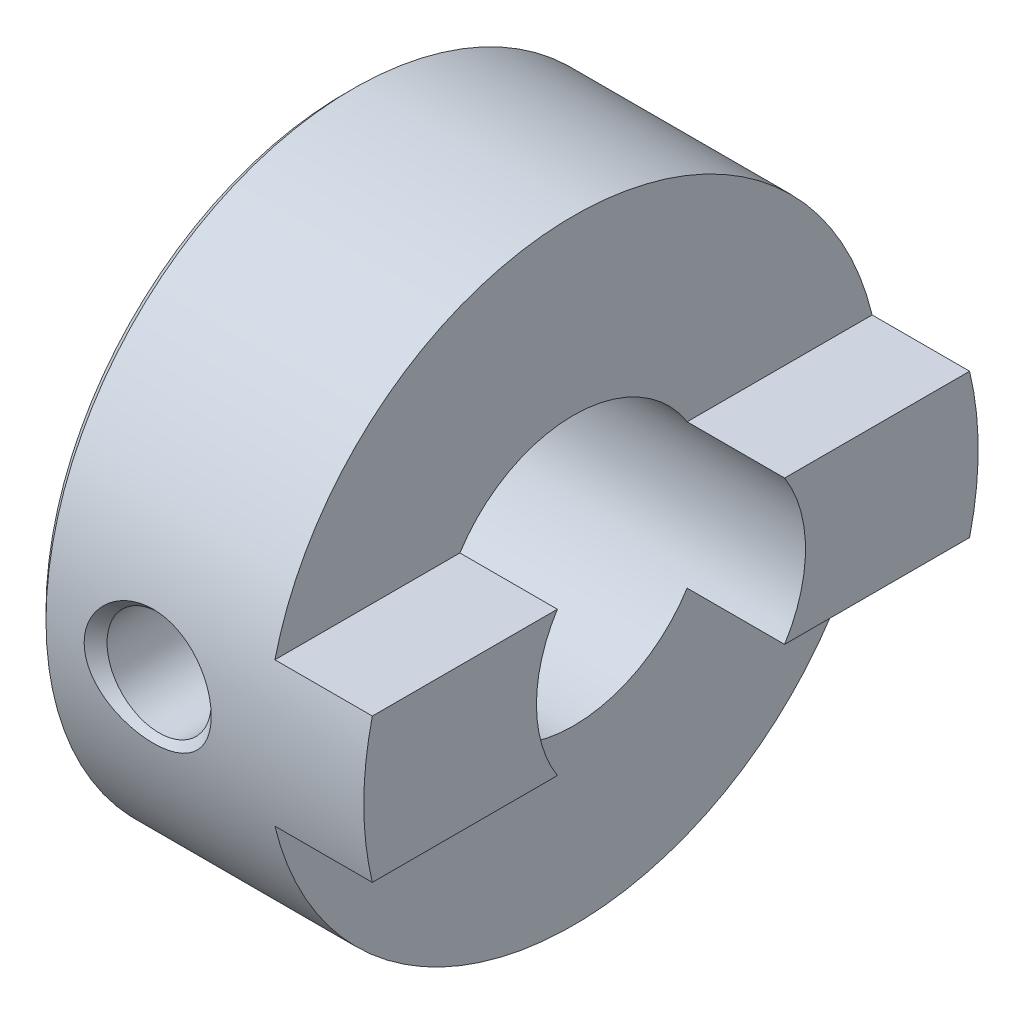
SolidWorks part; units mm, degrees
ref_plane "Front Plane" through (0, 0, 0) normal (0, 0, 1) x (1, 0, 0)
ref_plane "Top Plane" through (0, 0, 0) normal (0, 1, 0) x (1, 0, 0)
ref_plane "Right Plane" through (0, 0, 0) normal (1, 0, 0) x (0, 0, -1)
ref_plane "Plane1" through (0, 0, 0) normal (0, 0, 1) x (1, 0, 0)
sketch "Sketch1" plane through (0, 0, 0) normal (0, 0, 1) x (1, 0, 0)
  line L0 (0, 7.05) -> (0, 3.175)
  line L1 (0, 3.175) -> (7.7, 3.175)
  line L2 (7.7, 3.175) -> (7.7, 7.25)
  line L3 (7.7, 7.25) -> (0.2, 7.25)
  line L4 (0.2, 7.25) -> (0, 7.05)
  line L5 (7.7, 0) -> (0, 0) construction
revolve "Revolve1" add sketch "Sketch1" angle 360 about L5
ref_plane "Plane2" through (7.7, 0, 0) normal (1, 0, 0) x (0, 0, -1)
sketch "Sketch2" plane through (7.7, 0, 0) normal (1, 0, 0) x (0, 0, -1)
  line L0 (-8.25, 7.75) -> (-8.25, -7.75)
  line L1 (-8.25, -7.75) -> (8.25, -7.75)
  line L2 (8.25, -7.75) -> (8.25, 7.75)
  line L3 (8.25, 7.75) -> (-8.25, 7.75)
  line L4 (-7.25, 1.7) -> (-7.25, -1.7)
  line L5 (-7.25, -1.7) -> (7.25, -1.7)
  line L6 (7.25, -1.7) -> (7.25, 1.7)
  line L7 (7.25, 1.7) -> (-7.25, 1.7)
extrude "Cut-Extrude1" cut sketch "Sketch2" against normal blind 2.3
ref_plane "Plane3" through (2.6, 0, 0) normal (1, 0, 0) x (0, 0, -1)
sketch "Sketch3" plane through (2.6, 0, 0) normal (1, 0, 0) x (0, 0, -1)
  line L0 (-7.25, 0) -> (-7.25, 1.5)
  line L1 (-7.25, 1.5) -> (-6.9795, 1.2295)
  line L2 (-6.9795, 1.2295) -> (0, 1.2295)
  line L3 (0, 1.2295) -> (0, 0)
  line L4 (0, 0) -> (-7.25, 0)
  line L5 (0, 0) -> (-7.25, 0) construction
revolve "Cut-Revolve1" cut sketch "Sketch3" angle 360 about L5
ref_plane "Plane4" through (2.6, 0, 0) normal (1, 0, 0) x (0, 0, -1)
sketch "Sketch4" plane through (2.6, 0, 0) normal (1, 0, 0) x (0, 0, -1)
  line L0 (0, -7.25) -> (-1.5, -7.25)
  line L1 (-1.5, -7.25) -> (-1.2295, -6.9795)
  line L2 (-1.2295, -6.9795) -> (-1.2295, 0)
  line L3 (-1.2295, 0) -> (0, 0)
  line L4 (0, 0) -> (0, -7.25)
  line L5 (0, 0) -> (0, -7.25) construction
revolve "Cut-Revolve2" cut sketch "Sketch4" angle 360 about L5
